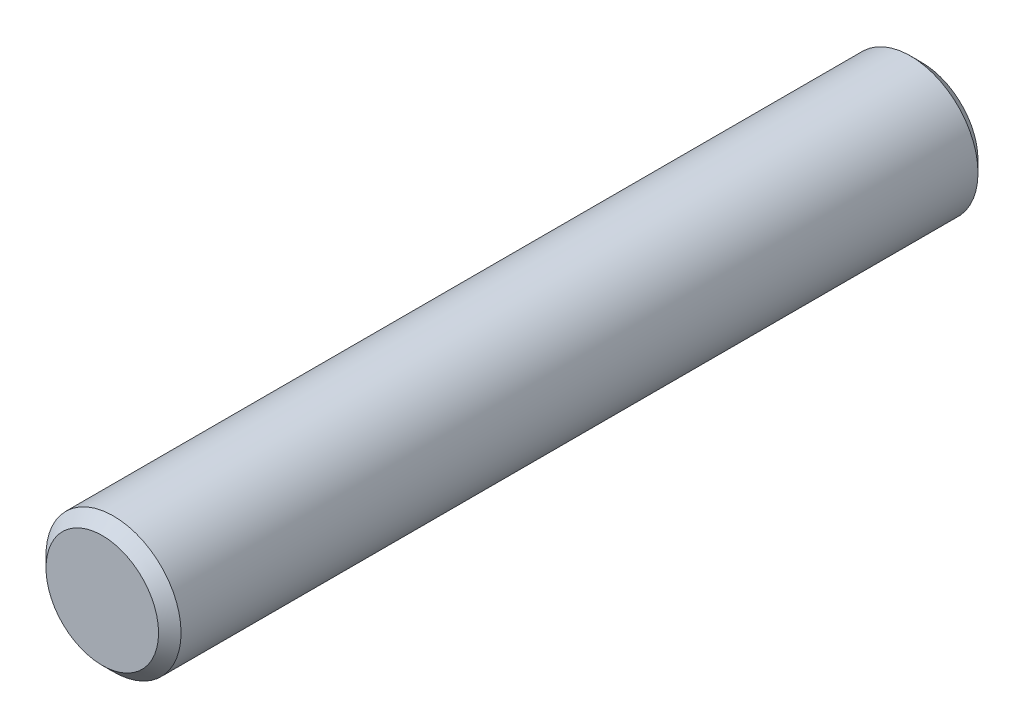
SolidWorks part; units mm, degrees
material "AISI 1020"
ref_plane "Front Plane" through (0, 0, 0) normal (0, 0, 1) x (1, 0, 0)
ref_plane "Top Plane" through (0, 0, 0) normal (0, 1, 0) x (1, 0, 0)
ref_plane "Right Plane" through (0, 0, 0) normal (1, 0, 0) x (0, 0, -1)
sketch "Sketch1" plane through (0, 0, 0) normal (0, 0, 1) x (1, 0, 0)
  circle A0 centre (0, 0) radius 3
  dimension "D1" = 6
extrude "Boss-Extrude1" add sketch "Sketch1" along normal blind 36.401
chamfer "Chamfer1" distance 0.5 angle 45 2 edges at (3, 0, 0) (3, 0, 36.401)
